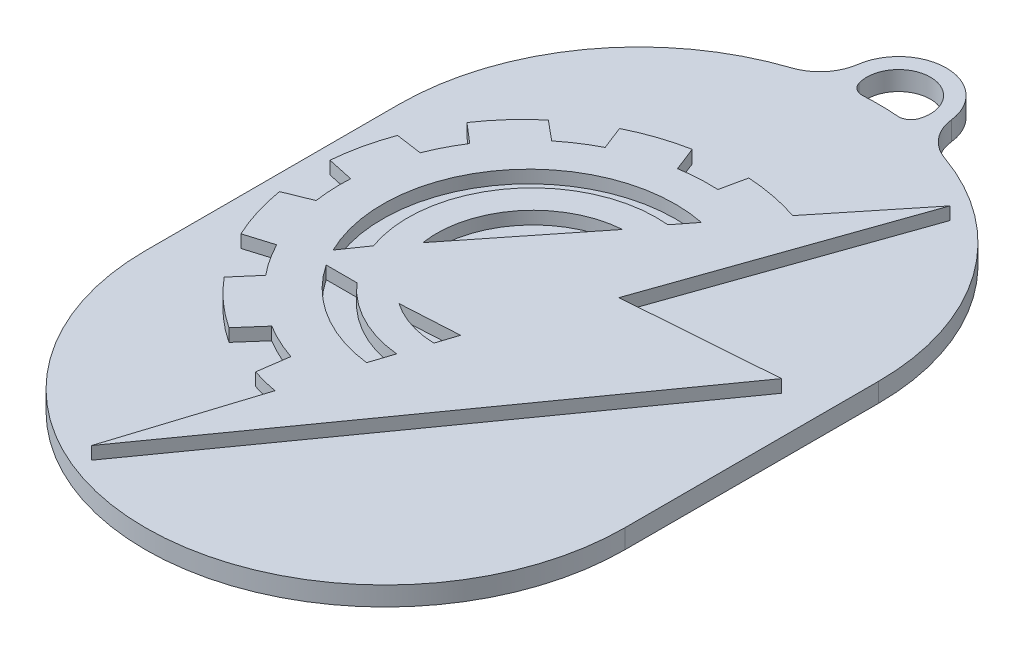
SolidWorks part; units mm, degrees
ref_plane "Plano frontal" through (0, 0, 0) normal (0, 0, 1) x (1, 0, 0)
ref_plane "Plano superior" through (0, 0, 0) normal (0, 1, 0) x (1, 0, 0)
ref_plane "Plano direito" through (0, 0, 0) normal (1, 0, 0) x (0, 0, -1)
sketch "Esboço1" plane through (0, 0, 0) normal (0, 1, 0) x (1, 0, 0)
  line L0 (16.3106, 52.7829) -> (81.553, 52.7829) construction
  line L1 (35.3689, 1.5585) -> (80.4496, 64.8478)
  line L2 (80.4496, 64.8478) -> (56.6611, 63.0857)
  line L3 (56.6611, 63.0857) -> (70.1706, 101.5585)
  line L4 (35.3689, 1.5585) -> (42.3114, 23.4092)
  line L5 (59.1567, 87.902) -> (70.1706, 101.5585)
  line L6 (38.2214, 24.4583) -> (38.9166, 29.2914)
  line L7 (30.1206, 28.365) -> (33.2616, 31.9443)
  line L8 (18.2862, 42.0842) -> (22.5903, 43.3944)
  line L9 (22.8608, 34.8731) -> (25.8779, 38.3786)
  line L10 (15.5792, 50.8577) -> (19.6675, 52.5117)
  line L11 (15.2682, 59.0927) -> (19.4081, 58.1957)
  line L12 (17.2032, 67.7703) -> (21.347, 67.1858)
  line L13 (20.9021, 74.9739) -> (23.9782, 72.3389)
  line L14 (26.9508, 81.7087) -> (30.0653, 79.134)
  line L15 (33.6963, 86.1468) -> (35.1472, 82.4424)
  line L16 (42.2387, 89.0292) -> (43.7186, 85.2422)
  line L17 (49.7251, 85.574) -> (50.5905, 89.5683)
  line L18 (45.6922, 34.4215) -> (46.8526, 37.9786)
  line L19 (48.3105, 42.3586) -> (49.3456, 45.5317)
  line L20 (49.3456, 45.5317) -> (40.1841, 45.0096)
  line L21 (33.7769, 55.1597) -> (47.6689, 72.6514)
  line L22 (34.0507, 44.5332) -> (29.2282, 44.5332)
  line L23 (30.3331, 50.8577) -> (27.7435, 47.1165)
  line L24 (50.5964, 76.8487) -> (52.9063, 79.8038)
  arc A2 (42.3114, 23.4092) -> (38.2214, 24.4583) centre (48.5496, 56.2261) cw
  arc A3 (38.9166, 29.2914) -> (33.2616, 31.9443) centre (48.3096, 56.6667) cw
  arc A4 (45.6922, 34.4215) -> (29.2282, 44.5332) centre (48.3809, 57.2586) cw
  arc A5 (46.8526, 37.9786) -> (34.0507, 44.5332) centre (48.7245, 57.4137) cw
  arc A6 (48.3105, 42.3586) -> (40.1841, 45.0096) centre (48.7613, 57.5213) cw
  arc A7 (30.1206, 28.365) -> (22.8608, 34.8731) centre (48.5496, 56.2261) cw
  arc A8 (18.2862, 42.0842) -> (15.5792, 50.8577) centre (48.5496, 56.2261) cw
  arc A9 (25.8779, 38.3786) -> (22.5903, 43.3944) centre (48.3096, 56.6667) cw
  arc A10 (15.2682, 59.0927) -> (17.2032, 67.7703) centre (48.5496, 56.2261) cw
  arc A11 (19.6675, 52.5117) -> (19.4081, 58.1957) centre (48.3096, 56.6667) cw
  arc A12 (20.9021, 74.9739) -> (26.9508, 81.7087) centre (48.5496, 56.2261) cw
  arc A13 (21.347, 67.1858) -> (23.9782, 72.3389) centre (48.3096, 56.6667) cw
  arc A14 (33.6963, 86.1468) -> (42.2387, 89.0292) centre (48.5496, 56.2261) cw
  arc A15 (30.0653, 79.134) -> (35.1472, 82.4424) centre (48.3096, 56.6667) cw
  arc A16 (50.5905, 89.5683) -> (59.1567, 87.902) centre (48.5496, 56.2261) cw
  arc A17 (43.7186, 85.2422) -> (49.7251, 85.574) centre (48.3096, 56.6667) cw
  arc A18 (33.7769, 55.1597) -> (47.6689, 72.6514) centre (48.7613, 57.5213) cw
  arc A19 (27.7435, 47.1165) -> (52.9063, 79.8038) centre (48.3809, 57.2586) cw
  arc A20 (30.3331, 50.8577) -> (50.5964, 76.8487) centre (48.7245, 57.4137) cw
  dimension "D1" = 100
extrude "Ressalto-extrusão1" add sketch "Esboço1" along normal blind 2
sketch "Esboço3" plane through (0, 0, 0) normal (0, -1, 0) x (1, 0, 0)
  line L0 (48.7613, -74.1265) -> (48.7613, -34.2669) construction
  line L7 (11.0842, -74.1265) -> (11.0842, -34.2669)
  line L8 (86.4384, -74.1265) -> (86.4384, -34.2669)
  arc A0 (11.0842, -74.1265) -> (86.4384, -74.1265) centre (48.7613, -74.1265) ccw
  arc A1 (86.4384, -34.2669) -> (11.0842, -34.2669) centre (48.7613, -34.2669) ccw
  arc A2 (45.6922, -34.4215) -> (29.2282, -44.5332) centre (48.3809, -57.2586) ccw construction
  point P1 (48.7613, -54.1967)
  point P7 (48.3787, -29.4729)
  point P8 (43.9865, -88.9759)
  point P10 (93.0271, -61.4437)
  point P11 (0, 0)
  point P12 (43.4257, -67.3086)
  point P13 (44.0567, -34.674)
  point P17 (48.7613, -74.1265)
extrude "Ressalto-extrusão2" add sketch "Esboço3" along normal blind 3
sketch "Esboço4" plane through (0, 0, 0) normal (0, 1, 0) x (1, 0, 0)
  circle A2 centre (49.1294, 114.5628) radius 5
  circle A4 centre (49.1294, 114.5628) radius 7.5
  point P2 (49.1294, 114.5628)
  point P6 (0, 0)
extrude "Ressalto-extrusão3" add sketch "Esboço4" against normal blind 3
fillet "Filete4" radius 7 2 edges at (42.3949, -1.5, -111.2619) (55.8027, -1.5, -111.1398)
fillet "Filete5" radius 2 2 edges at (45.0844, -1.5, -111.6238) (53.1203, -1.5, -111.5506)
